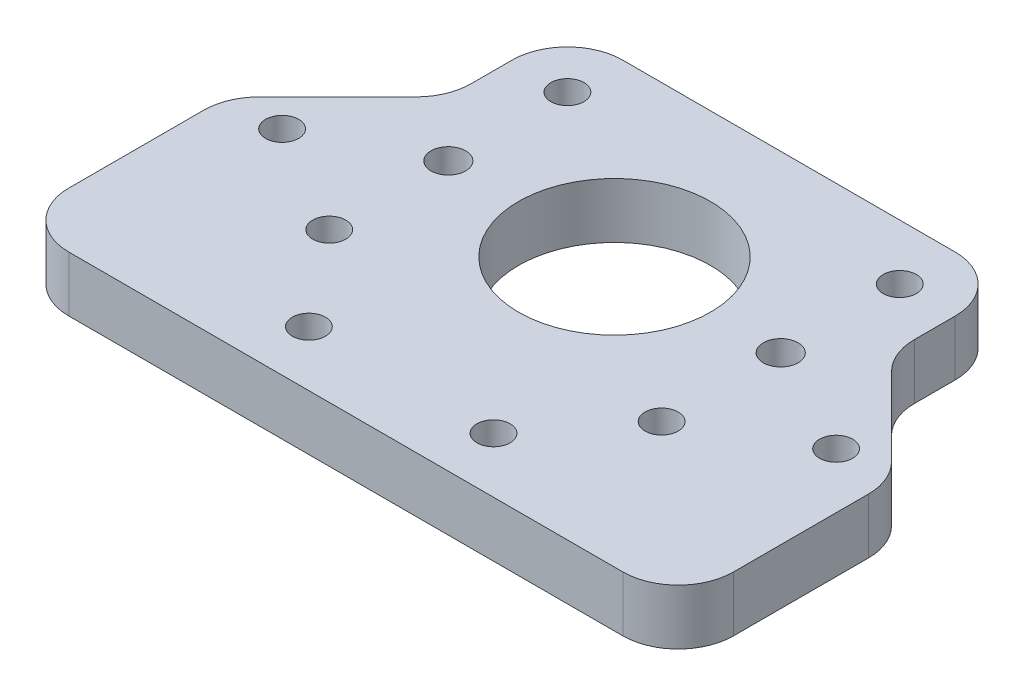
SolidWorks part; units mm, degrees
material "Balsa"
ref_plane "Front" through (0, 0, 0) normal (0, 0, 1) x (1, 0, 0)
ref_plane "Top" through (0, 0, 0) normal (0, 1, 0) x (1, 0, 0)
ref_plane "Right" through (0, 0, 0) normal (1, 0, 0) x (0, 0, -1)
sketch "Sketch1" plane through (0, 0, 0) normal (0, 1, 0) x (1, 0, 0)
  line L0 (38.1, 0) -> (38.1, 200) construction
  line L1 (0, 0) -> (76.2, 0)
  line L2 (0, 0) -> (0, 50.8)
  line L3 (0, 50.8) -> (38.1, 50.8)
  line L4 (38.1, 50.8) -> (76.2, 50.8)
  line L5 (38.1, 38.65) -> (79.051, 38.65) construction
  line L6 (38.1, 37.15) -> (79.051, 37.15) construction
  line L7 (76.2, 50.8) -> (76.2, 0)
  circle A0 centre (38.1, 118.65) radius 80 construction
  circle A1 centre (38.1, 30.8) radius 6.35 construction
  circle A2 centre (38.1, 30.8) radius 20 construction
  circle A4 centre (38.1, 30.8) radius 11
  dimension "D3" = 160
  dimension "D4" = 12.7
  dimension "D5" = 50.8
  dimension "D8" = 22
  dimension "D2" = 40
  dimension "D1" = 1.5
  dimension "D6" = 76.2
extrude "Boss-Extrude1" add sketch "Sketch1" along normal blind 6.35
sketch "Sketch2" plane through (0, 6.35, 0) normal (0, 1, 0) x (1, 0, 0)
  line L0 (38.1, 50.8) -> (38.1, 0) construction
  line L2 (0, 30.8) -> (76.2, 30.8) construction
  line L5 (76.2, 0) -> (76.2, 50.8) construction
  line L6 (76.2, 50.8) -> (0, 50.8) construction
  line L8 (0, 0) -> (76.2, 0) construction
  line L9 (0, 50.8) -> (0, 0) construction
  circle A1 centre (19.05, 30.8) radius 1.9939
  circle A4 centre (57.15, 30.8) radius 1.9939
  point P26 (38.1, 30.8)
  dimension "D1" = 3.9878
  dimension "D2" = 19.05
extrude "Cut-Extrude1" cut sketch "Sketch2" against normal through all
sketch "Sketch14" plane through (0, 0, 0) normal (0, -1, 0) x (1, 0, 0)
  line L0 (38.1, -30.8) -> (3.391, -30.8) construction
  line L2 (38.1, -30.8) -> (38.1, -33.65) construction
  line L3 (19.05, -17.15) -> (57.15, -17.15) construction
  line L5 (57.15, -44.45) -> (19.05, -44.45) construction
  line L7 (76.2, -50.8) -> (0, -50.8) construction
  line L8 (57.15, -30.8) -> (38.1, -30.8) construction
  circle A0 centre (38.1, -30.8) radius 11 construction
  circle A1 centre (57.15, -44.45) radius 1.8986
  circle A2 centre (19.05, -44.45) radius 1.8986
  circle A3 centre (19.05, -17.15) radius 1.8986
  circle A4 centre (57.15, -17.15) radius 1.8986
  circle A5 centre (57.15, -30.8) radius 1.9939 construction
  point P0 (57.15, -44.45)
  point P12 (19.05, -44.45)
  point P13 (19.05, -17.15)
  point P14 (57.15, -17.15)
  dimension "D3" = 3.7973
  dimension "D1" = 19.05
  dimension "D2" = 6.35
extrude "M3-tap" cut sketch "Sketch14" against normal through all
sketch "Sketch15" plane through (0, 0, 0) normal (0, -1, 0) x (1, 0, 0)
  line L0 (38.1, 0) -> (38.1, -48.7422) construction
  line L2 (76.2, 0) -> (76.2, -50.8) construction
  line L3 (0, 0) -> (76.2, 0) construction
  line L5 (76.2, -24.45) -> (69.85, -24.45) construction
  line L10 (69.85, -24.45) -> (69.85, 0) construction
  line L14 (69.85, -6.35) -> (48.6833, -6.35) construction
  line L15 (48.6833, -6.35) -> (27.5167, -6.35) construction
  line L16 (27.5167, -6.35) -> (6.35, -6.35) construction
  circle A0 centre (69.85, -24.45) radius 1.8987
  circle A1 centre (69.85, -6.35) radius 1.8987 construction
  circle A2 centre (48.6833, -6.35) radius 1.8986
  circle A3 centre (27.5167, -6.35) radius 1.8986
  circle A4 centre (6.35, -6.35) radius 1.8986 construction
  circle A5 centre (6.35, -24.45) radius 1.8986
  point P0 (69.85, -24.45)
  point P1 (69.85, -6.35)
  point P35 (6.35, -6.35)
  point P36 (6.35, -24.45)
  point P42 (48.6833, -6.35)
  point P50 (27.5167, -6.35)
  dimension "D4" = 3.7973
  dimension "D1" = 6.35
  dimension "D2" = 6.35
  dimension "D3" = 24.45
extrude "M5-through" cut sketch "Sketch15" against normal through all
sketch "Sketch12" plane through (0, 6.35, 0) normal (0, 1, 0) x (1, 0, 0)
  line L1 (0, 50.8) -> (12.7, 50.8)
  line L2 (0, 50.8) -> (0, 24.45)
  line L4 (12.7, 50.8) -> (12.7, 37.15)
  line L5 (38.1, 30.8) -> (38.1, 50.8) construction
  line L6 (76.2, 50.8) -> (0, 50.8) construction
  line L7 (63.5, 50.8) -> (63.5, 37.15)
  line L8 (76.2, 24.45) -> (63.5, 37.15)
  line L9 (76.2, 50.8) -> (76.2, 24.45)
  line L10 (76.2, 50.8) -> (63.5, 50.8)
  line L11 (12.7, 37.15) -> (0, 24.45)
  line L12 (0, 50.8) -> (0, 0) construction
  circle A1 centre (19.05, 44.45) radius 1.8987 construction
  dimension "D1" = 6.35
  dimension "D2" = 13.65
  dimension "D3" = 45
extrude "Cut-Extrude2" cut sketch "Sketch12" against normal through all
fillet "Fillet2" radius 6.35 8 edges at (76.2, 3.175, 0) (0, 3.175, 0) (76.2, 3.175, -24.45) (63.5, 3.175, -37.15) (63.5, 3.175, -50.8) (12.7, 3.175, -50.8) (0, 3.175, -24.45) (12.7, 3.175, -37.15)
sketch "Sketch13" [suppressed] plane through (0, 0, 0) normal (0, -1, 0) x (1, 0, 0)
  line L0 (69.85, -24.45) -> (69.85, -6.35) construction
  line L1 (69.85, -6.35) -> (6.35, -6.35) construction
  line L2 (6.35, -6.35) -> (6.35, -24.45) construction
  circle A0 centre (69.85, -15.4) radius 1.5
  circle A1 centre (38.1, -6.35) radius 1.5
  circle A2 centre (6.35, -15.4) radius 1.5
  dimension "D1" = 3
extrude "Cut-Extrude3" [suppressed] cut sketch "Sketch13" against normal through all
other "Move Face1" [suppressed] parameters "D1"=0.08
